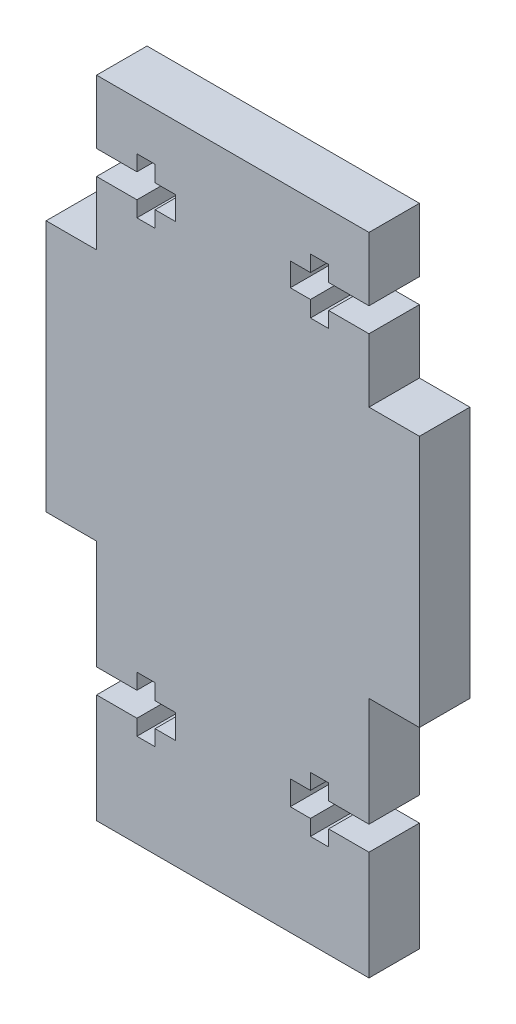
SolidWorks part; units mm, degrees
material "Acrylic (Medium-high impact)"
ref_plane "Front Plane" through (0, 0, 0) normal (0, 0, 1) x (1, 0, 0)
ref_plane "Top Plane" through (0, 0, 0) normal (0, 1, 0) x (1, 0, 0)
ref_plane "Right Plane" through (0, 0, 0) normal (1, 0, 0) x (0, 0, -1)
sketch "Sketch1" plane through (0, 0, 0) normal (0, 0, 1) x (1, 0, 0)
  line L0 (0, 0) -> (0, 64) construction
  line L1 (-13.5, 0) -> (13.5, 0)
  line L2 (13.5, 0) -> (13.5, 24)
  line L3 (13.5, 24) -> (18.5, 24)
  line L4 (18.5, 24) -> (18.5, 49)
  line L5 (18.5, 49) -> (13.5, 49)
  line L6 (13.5, 49) -> (13.5, 64)
  line L7 (13.5, 64) -> (-13.5, 64)
  line L8 (-13.5, 49) -> (-13.5, 64)
  line L9 (-18.5, 49) -> (-13.5, 49)
  line L10 (-18.5, 24) -> (-18.5, 49)
  line L11 (-13.5, 24) -> (-18.5, 24)
  line L12 (-13.5, 0) -> (-13.5, 24)
  dimension "D1" = 15
  dimension "D2" = 25
  dimension "D3" = 24
  dimension "D4" = 5
  dimension "D5" = 13.5
extrude "Boss-Extrude1" add sketch "Sketch1" along normal blind 5
sketch "Sketch2" plane through (0, 0, 5) normal (0, 0, 1) x (1, 0, 0)
  line L0 (-13.5, 56.5) -> (13.5, 56.5) construction
  line L1 (-13.5, 64) -> (-13.5, 49) construction
  line L2 (13.5, 49) -> (13.5, 64) construction
  line L3 (-13.5, 56.5) -> (-13.5, 57.7)
  line L4 (-13.5, 57.7) -> (-9.5, 57.7)
  line L5 (-9.5, 57.7) -> (-9.5, 59.25)
  line L6 (-9.5, 59.25) -> (-7.7, 59.25)
  line L7 (-7.7, 59.25) -> (-7.7, 57.6542)
  line L8 (-7.7, 57.6542) -> (-5.7, 57.6542)
  line L9 (-5.7, 57.6542) -> (-5.7, 55.3458)
  line L10 (-7.7, 55.3458) -> (-5.7, 55.3458)
  line L11 (-7.7, 53.75) -> (-7.7, 55.3458)
  line L12 (-9.5, 53.75) -> (-7.7, 53.75)
  line L13 (-9.5, 55.3) -> (-9.5, 53.75)
  line L14 (-13.5, 55.3) -> (-9.5, 55.3)
  line L15 (-13.5, 56.5) -> (-13.5, 55.3)
  line L16 (0, 64) -> (0, 0) construction
  line L17 (13.5, 64) -> (-13.5, 64) construction
  line L18 (-13.5, 0) -> (13.5, 0) construction
  line L19 (13.5, 56.5) -> (13.5, 55.3)
  line L20 (13.5, 55.3) -> (9.5, 55.3)
  line L21 (9.5, 55.3) -> (9.5, 53.75)
  line L22 (9.5, 53.75) -> (7.7, 53.75)
  line L23 (7.7, 53.75) -> (7.7, 55.3458)
  line L24 (7.7, 55.3458) -> (5.7, 55.3458)
  line L25 (5.7, 57.6542) -> (5.7, 55.3458)
  line L26 (7.7, 57.6542) -> (5.7, 57.6542)
  line L27 (7.7, 59.25) -> (7.7, 57.6542)
  line L28 (9.5, 59.25) -> (7.7, 59.25)
  line L29 (9.5, 57.7) -> (9.5, 59.25)
  line L30 (13.5, 57.7) -> (9.5, 57.7)
  line L31 (13.5, 56.5) -> (13.5, 57.7)
  line L32 (-13.5, 12) -> (13.5, 12) construction
  line L33 (-13.5, 24) -> (-13.5, 0) construction
  line L34 (13.5, 0) -> (13.5, 24) construction
  line L35 (-13.5, 10.8) -> (-13.5, 13.2)
  line L36 (-13.5, 13.2) -> (-9.5, 13.2)
  line L37 (-9.5, 13.2) -> (-9.5, 14.75)
  line L38 (-9.5, 14.75) -> (-7.7, 14.75)
  line L39 (-7.7, 14.75) -> (-7.7, 13.2)
  line L40 (-7.7, 13.2) -> (-5.7, 13.2)
  line L41 (-5.7, 13.2) -> (-5.7, 10.8)
  line L42 (-7.7, 10.8) -> (-5.7, 10.8)
  line L43 (-7.7, 9.25) -> (-7.7, 10.8)
  line L44 (-9.5, 9.25) -> (-7.7, 9.25)
  line L45 (-9.5, 10.8) -> (-9.5, 9.25)
  line L46 (-13.5, 10.8) -> (-9.5, 10.8)
  line L47 (13.5, 10.8) -> (9.5, 10.8)
  line L48 (9.5, 10.8) -> (9.5, 9.25)
  line L49 (9.5, 9.25) -> (7.7, 9.25)
  line L50 (7.7, 9.25) -> (7.7, 10.8)
  line L51 (7.7, 10.8) -> (5.7, 10.8)
  line L52 (5.7, 13.2) -> (5.7, 10.8)
  line L53 (7.7, 13.2) -> (5.7, 13.2)
  line L54 (7.7, 14.75) -> (7.7, 13.2)
  line L55 (9.5, 14.75) -> (7.7, 14.75)
  line L56 (9.5, 13.2) -> (9.5, 14.75)
  line L57 (13.5, 13.2) -> (9.5, 13.2)
  line L58 (13.5, 10.8) -> (13.5, 13.2)
  point P15 (-5.7, 56.5)
  point P41 (5.7, 56.5)
  point P56 (-5.7, 12)
  point P73 (5.7, 12)
  dimension "D1" = 4
  dimension "D2" = 1.8
  dimension "D3" = 2
  dimension "D4" = 2.4
  dimension "D5" = 5.5
  dimension "D6" = 2.4
  dimension "D7" = 5.5
extrude "Cut-Extrude2" cut sketch "Sketch2" against normal through all
